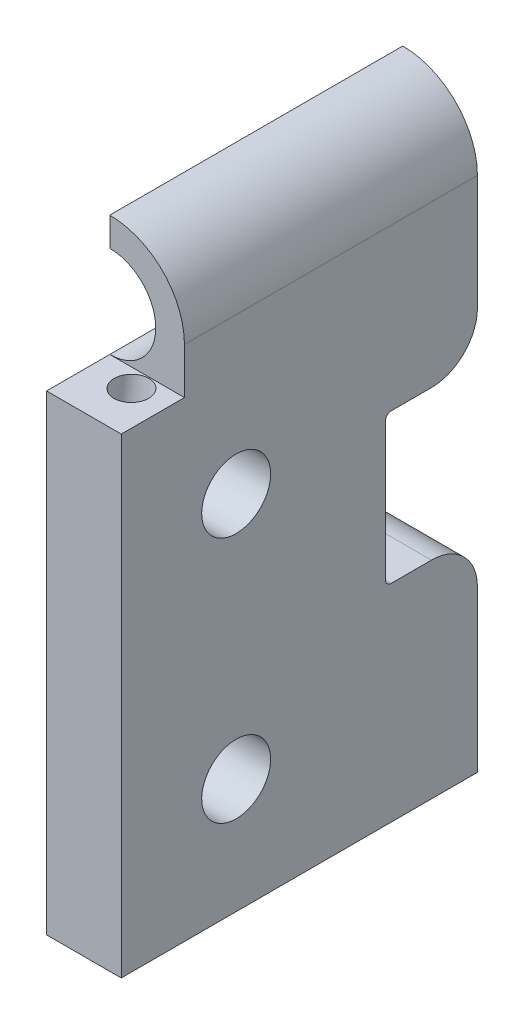
SolidWorks part; units mm, degrees
ref_plane "Front Plane" through (0, 0, 0) normal (0, 0, 1) x (1, 0, 0)
ref_plane "Top Plane" through (0, 0, 0) normal (0, 1, 0) x (1, 0, 0)
ref_plane "Right Plane" through (0, 0, 0) normal (1, 0, 0) x (0, 0, -1)
sketch "Sketch1" plane through (0, 0, 0) normal (0, 0, 1) x (1, 0, 0)
  line L0 (-3.75, 29) -> (-3.75, 22.5)
  line L2 (-3.75, 22.5) -> (-3.75, -22.5)
  line L3 (-3.75, -22.5) -> (2.75, -22.5)
  line L4 (2.75, 22.5) -> (2.75, -22.5)
  arc A0 (2.75, 22.5) -> (-3.75, 29) centre (-3.75, 22.5) ccw
  point P0 (0, 0)
  dimension "D1" = 6.5
  dimension "D2" = 45
extrude "Boss-Extrude1" add sketch "Sketch1" along normal blind 31
sketch "Sketch2" plane through (-3.75, 0, 0) normal (-1, 0, 0) x (0, 0, 1)
  line L5 (31, 29) -> (25.5, 29)
  line L6 (31, 29) -> (31, 18.5)
  line L7 (31, 18.5) -> (25.5, 18.5)
  line L8 (25.5, 29) -> (25.5, 18.5)
  dimension "D3" = 5.5
  dimension "D4" = 10.5
extrude "Cut-Extrude1" cut sketch "Sketch2" against normal through all
sketch "Sketch3" plane through (-3.75, 0, 0) normal (-1, 0, 0) x (0, 0, 1)
  line L0 (25.5, 29) -> (0, 29) construction
  line L1 (31, 18.5) -> (31, -22.5) construction
  line L3 (31, -22.5) -> (0, -22.5) construction
  circle A0 centre (21, 9) radius 3
  circle A1 centre (21, -12.5) radius 3
  dimension "D1" = 6
  dimension "D2" = 20
  dimension "D3" = 10
  dimension "D5" = 10
extrude "Cut-Extrude2" cut sketch "Sketch3" against normal through all
sketch "Sketch6" plane through (-3.75, 0, 0) normal (-1, 0, 0) x (0, 0, 1)
  line L1 (0, 8.5) -> (8, 8.5)
  line L2 (0, 8.5) -> (0, -4.5)
  line L3 (0, -4.5) -> (8, -4.5)
  line L4 (8, 8.5) -> (8, -4.5)
  line L6 (0, 29) -> (0, -22.5) construction
  line L7 (31, -22.5) -> (0, -22.5) construction
  dimension "D1" = 8
  dimension "D2" = 13
  dimension "D3" = 18
extrude "Cut-Extrude5" cut sketch "Sketch6" against normal up to next
fillet "Fillet1" radius 0.5 2 edges at (-0.5, -4.5, 8) (-0.5, 8.5, 8)
fillet "Fillet2" radius 4 2 edges at (-0.5, -4.5, 0) (-0.5, 8.5, 0)
sketch "Sketch8" plane through (0, 0, 25.5) normal (0, 0, 1) x (1, 0, 0)
  line L0 (-3.75, 29) -> (-3.75, 18.5) construction
  line L1 (2.75, 18.5) -> (-3.75, 18.5) construction
  line L2 (-3.75, 26.5) -> (-3.75, 18.5)
  arc A0 (-3.75, 18.5) -> (-3.75, 26.5) centre (-3.75, 22.5) ccw
  dimension "D1" = 4
  dimension "D2" = 4
extrude "Cut-Extrude7" cut sketch "Sketch8" against normal up to next
ref_plane "Plane2" through (0, 14.6273, -2.0557) normal (0, 0.9903, -0.1392) x (-1, 0, 0)
sketch "Sketch9" plane through (0, 14.6273, -2.0557) normal (0, 0.9903, -0.1392) x (-1, 0, 0)
  line L0 (-2.75, 27.8265) -> (-2.75, 33.273) construction
  line L1 (-2.75, 27.8265) -> (3.75, 27.8265) construction
  circle A0 centre (0.25, 29.4265) radius 1.5
  point P6 (-5.3016, 29.0023)
  point P9 (-5.4395, 29.7575)
  dimension "D1" = 3
  dimension "D2" = 3
  dimension "D3" = 1.6
extrude "Cut-Extrude8" cut sketch "Sketch9" against normal blind 17 contours A0
